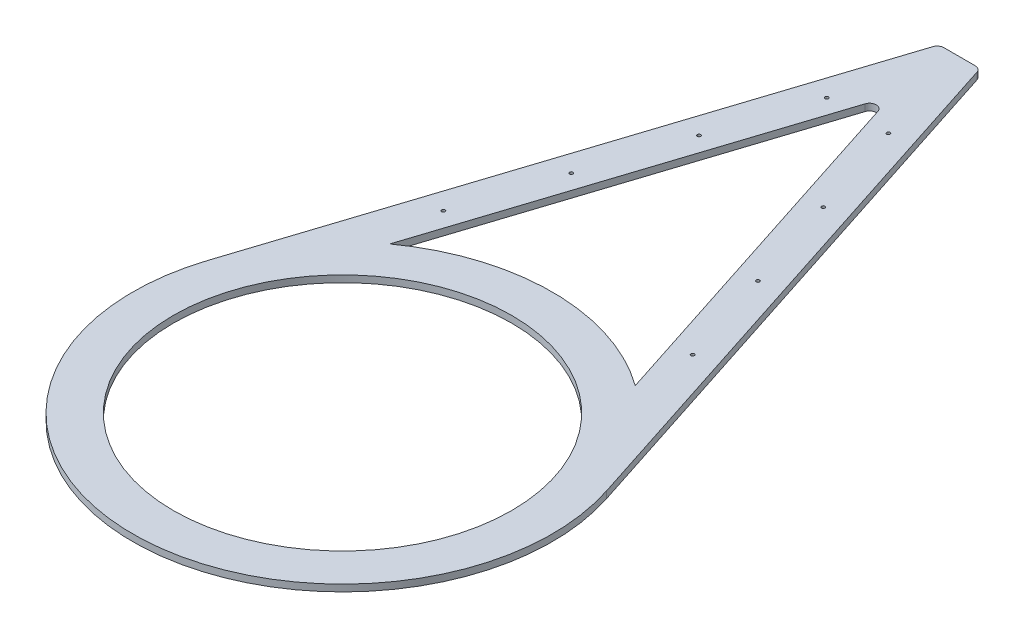
SolidWorks part; units mm, degrees
ref_plane "Front Plane" through (0, 0, 0) normal (0, 0, 1) x (1, 0, 0)
ref_plane "Top Plane" through (0, 0, 0) normal (0, 1, 0) x (1, 0, 0)
ref_plane "Right Plane" through (0, 0, 0) normal (1, 0, 0) x (0, 0, -1)
sketch "Sketch2" plane through (0, 0, 0) normal (0, 1, 0) x (1, 0, 0)
  line L0 (-294.8632, 95.4985) -> (-32.6272, 905.1838)
  line L1 (-23.1137, 912.1026) -> (23.1137, 912.1026)
  line L2 (0, 0) -> (0, 979.251) construction
  line L3 (-181.3884, 251.3216) -> (-9.5135, 782.0059)
  line L4 (294.8632, 95.4985) -> (30.3863, 912.1026)
  line L5 (181.3884, 251.3216) -> (9.5135, 782.0059)
  line L6 (0, 902.1026) -> (-251.9818, 124.0786) construction
  line L7 (0, 902.1026) -> (251.9818, 124.0786) construction
  circle A0 centre (0, 0) radius 250
  arc A1 (181.3884, 251.3216) -> (-181.3884, 251.3216) centre (0, 0) ccw
  arc A2 (-9.5135, 782.0059) -> (9.5135, 782.0059) centre (0, 778.9247) cw
  arc A3 (-294.8632, 95.4985) -> (294.8632, 95.4985) centre (0, 0) ccw
  arc A4 (-23.1137, 912.1026) -> (-32.6272, 905.1838) centre (-23.1137, 902.1026) ccw
  arc A5 (23.1137, 912.1026) -> (32.6272, 905.1838) centre (23.1137, 902.1026) cw
  circle A6 centre (-184.2103, 333.3311) radius 2.5
  circle A7 centre (-137.9928, 476.0334) radius 2.5
  circle A8 centre (-91.7752, 618.7357) radius 2.5
  circle A9 centre (-45.5576, 761.4379) radius 2.5
  circle A10 centre (45.5576, 761.4379) radius 2.5
  circle A11 centre (91.7752, 618.7357) radius 2.5
  circle A12 centre (137.9928, 476.0334) radius 2.5
  circle A13 centre (184.2103, 333.3311) radius 2.5
  point P15 (0, 811.3799)
  point P17 (-30.3863, 912.1026)
  point P21 (0, 912.1026)
  dimension "D1" = 500
  dimension "D2" = 10
  dimension "D3" = 10
  dimension "D4" = 5
  dimension "D5" = 150
  dimension "D6" = 150
  dimension "D7" = 150
extrude "Boss-Extrude1" add sketch "Sketch2" along normal blind 10 contours A5 L1 A4 L0 A3 L4 A12 A10 A9 A8 A7 A6 A0 L3 A2 L5 A1 A11 A13
